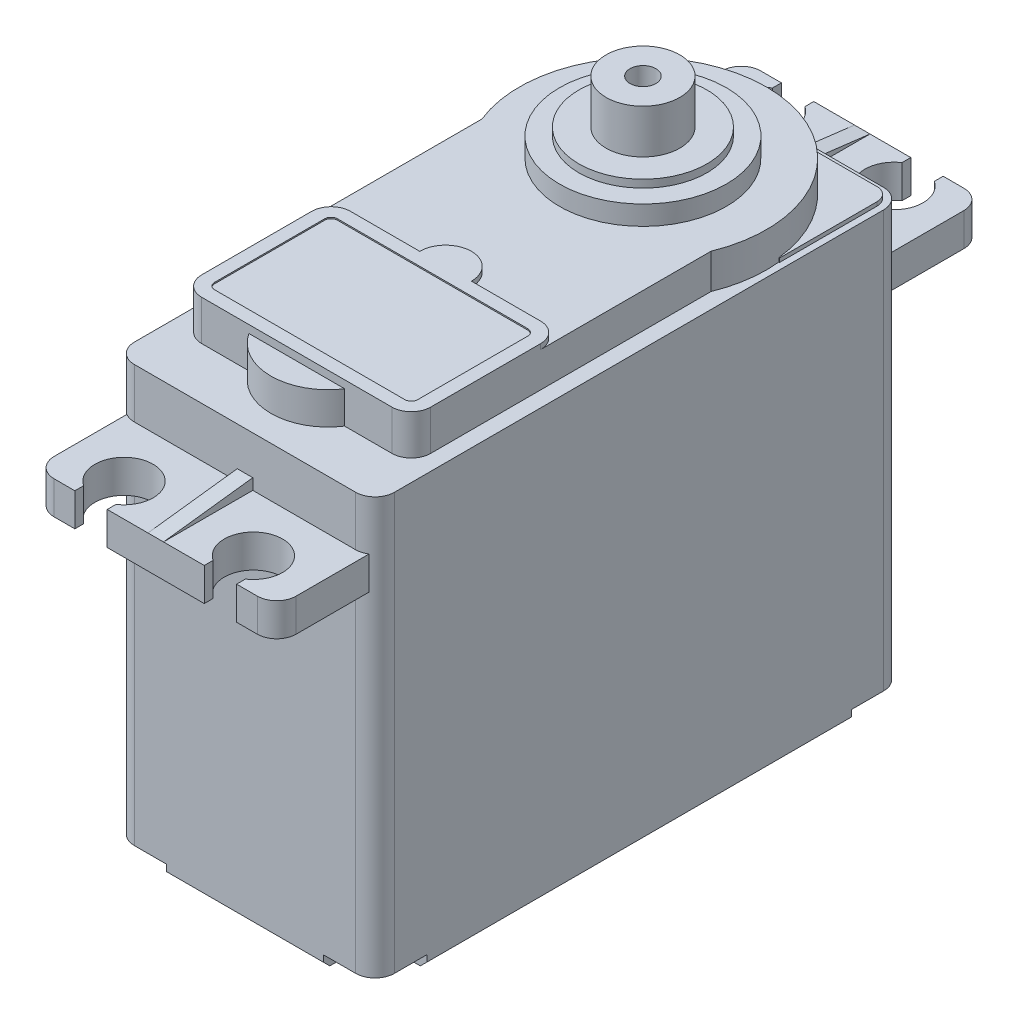
SolidWorks part; units mm, degrees
material "Feetech servo "
ref_plane "Front Plane" through (0, 0, 0) normal (0, 0, 1) x (1, 0, 0)
ref_plane "Top Plane" through (0, 0, 0) normal (0, 1, 0) x (1, 0, 0)
ref_plane "Right Plane" through (0, 0, 0) normal (1, 0, 0) x (0, 0, -1)
sketch "Sketch1" plane through (0, 0, 0) normal (0, 1, 0) x (1, 0, 0)
  line L0 (-10.05, -5.18) -> (10.05, -5.18) construction
  line L1 (-8.55, -25.58) -> (8.55, -25.58)
  line L2 (-10.05, -24.08) -> (-10.05, 13.72)
  line L3 (-8.55, 15.22) -> (8.55, 15.22)
  line L4 (10.05, -24.08) -> (10.05, 13.72)
  line L5 (-10.05, -25.58) -> (10.05, 15.22) construction
  line L6 (-10.05, 15.22) -> (10.05, -25.58) construction
  line L7 (0, -5.18) -> (0, 15.22) construction
  arc A0 (-10.05, 13.72) -> (-8.55, 15.22) centre (-8.55, 13.72) cw
  arc A1 (8.55, 15.22) -> (10.05, 13.72) centre (8.55, 13.72) cw
  arc A2 (10.05, -24.08) -> (8.55, -25.58) centre (8.55, -24.08) cw
  arc A3 (-8.55, -25.58) -> (-10.05, -24.08) centre (-8.55, -24.08) cw
  point P0 (0, 0)
  dimension "D5" = 1.5
  dimension "D1" = 20.1
  dimension "D2" = 40.8
  dimension "D3" = 25.58
extrude "Boss-Extrude1" add sketch "Sketch1" along normal blind 33.2
ref_plane "Plane1" through (0, 26.8, 0) normal (0, 1, 0) x (1, 0, 0)
sketch "Sketch4" plane through (0, 26.8, 0) normal (0, 1, 0) x (1, 0, 0)
  line L0 (-6.25, 22.12) -> (-6.25, 21.4408)
  line L1 (-7.85, -32.48) -> (-6.25, -32.48)
  line L2 (-9.35, -30.98) -> (-9.35, 20.62)
  line L3 (-7.85, 22.12) -> (-6.25, 22.12)
  line L4 (9.35, -30.98) -> (9.35, 20.62)
  line L5 (-9.35, -32.48) -> (9.35, 22.12) construction
  line L6 (-9.35, 22.12) -> (9.35, -32.48) construction
  line L7 (-3.75, 22.12) -> (-3.75, 21.4408)
  line L8 (-3.75, 22.12) -> (3.75, 22.12)
  line L9 (-10.05, -5.18) -> (10.05, -5.18) construction
  line L10 (6.25, 22.12) -> (7.85, 22.12)
  line L11 (6.25, -32.48) -> (6.25, -31.8008)
  line L12 (3.75, -32.48) -> (3.75, -31.8008)
  line L13 (0, -25.58) -> (0, 15.22) construction
  line L14 (-8.55, -25.58) -> (8.55, -25.58) construction
  line L15 (8.55, 15.22) -> (-8.55, 15.22) construction
  line L16 (-3.75, -32.48) -> (3.75, -32.48)
  line L17 (3.75, 22.12) -> (3.75, 21.4408)
  line L18 (6.25, 22.12) -> (6.25, 21.4408)
  line L19 (-3.75, -32.48) -> (-3.75, -31.8008)
  line L20 (-6.25, -32.48) -> (-6.25, -31.8008)
  line L21 (6.25, -32.48) -> (7.85, -32.48)
  line L22 (-10.05, 13.72) -> (-10.05, -24.08) construction
  arc A0 (7.85, 22.12) -> (9.35, 20.62) centre (7.85, 20.62) cw
  arc A1 (9.35, -30.98) -> (7.85, -32.48) centre (7.85, -30.98) cw
  arc A2 (-7.85, -32.48) -> (-9.35, -30.98) centre (-7.85, -30.98) cw
  arc A3 (-9.35, 20.62) -> (-7.85, 22.12) centre (-7.85, 20.62) cw
  arc A4 (-6.25, 21.4408) -> (-3.75, 21.4408) centre (-5, 19.57) ccw
  arc A5 (6.25, -31.8008) -> (3.75, -31.8008) centre (5, -29.93) ccw
  arc A6 (6.25, 21.4408) -> (3.75, 21.4408) centre (5, 19.57) cw
  arc A7 (-6.25, -31.8008) -> (-3.75, -31.8008) centre (-5, -29.93) cw
  point P0 (0, -5.18)
  dimension "D3" = 1.5
  dimension "D4" = 2.5
  dimension "D5" = 2.25
  dimension "D1" = 18.7
  dimension "D6" = 0.6792
  dimension "D7" = 10
  dimension "D8" = 49.5
extrude "Boss-Extrude2" add sketch "Sketch4" along normal blind 2.55
sketch "Sketch16" plane through (0, 33.2, 0) normal (0, 1, 0) x (1, 0, 0)
  line L0 (-9.55, 6.17) -> (9.55, 6.17)
  line L1 (0, 14.72) -> (0, -2.38) construction
  line L8 (-9.55, 13.72) -> (-9.55, -24.08)
  line L9 (-8.55, -25.08) -> (8.55, -25.08)
  line L10 (9.55, -24.08) -> (9.55, 13.72)
  line L11 (8.55, 14.72) -> (-8.55, 14.72)
  line L12 (-9.55, 13.72) -> (-9.55, -24.08)
  line L13 (-8.55, -25.08) -> (8.55, -25.08)
  line L14 (9.55, -24.08) -> (9.55, 13.72)
  line L15 (8.55, 14.72) -> (-8.55, 14.72)
  arc A8 (-8.55, 14.72) -> (-9.55, 13.72) centre (-8.55, 13.72) ccw
  arc A9 (-9.55, -24.08) -> (-8.55, -25.08) centre (-8.55, -24.08) ccw
  arc A10 (8.55, -25.08) -> (9.55, -24.08) centre (8.55, -24.08) ccw
  arc A11 (9.55, 13.72) -> (8.55, 14.72) centre (8.55, 13.72) ccw
  arc A12 (-8.55, 14.72) -> (-9.55, 13.72) centre (-8.55, 13.72) ccw
  arc A13 (-9.55, -24.08) -> (-8.55, -25.08) centre (-8.55, -24.08) ccw
  arc A14 (8.55, -25.08) -> (9.55, -24.08) centre (8.55, -24.08) ccw
  arc A15 (9.55, 13.72) -> (8.55, 14.72) centre (8.55, 13.72) ccw
  point P4 (0, 6.17)
  dimension "D1" = 0.5
extrude "Boss-Extrude11" add sketch "Sketch16" along normal blind 0.3 contours L1 L15 A12 L12 L0 | L15 L1 L0 L14 A15
sketch "Sketch5" plane through (0, 33.2, 0) normal (0, 1, 0) x (1, 0, 0)
  line L0 (8.55, -25.58) -> (-8.55, -25.58) construction
  line L1 (9.55, 6.17) -> (9.55, 13.72) construction
  line L2 (-8.85, 1.5811) -> (-8.85, -20.08)
  line L3 (-7.35, -21.58) -> (7.35, -21.58)
  line L4 (8.85, 1.5811) -> (8.85, -20.08)
  line L5 (-9.55, 13.72) -> (-9.55, 6.17) construction
  line L6 (0, 5.17) -> (0, -21.58) construction
  line L7 (8.55, 14.72) -> (-8.55, 14.72) construction
  arc A0 (8.85, 1.5811) -> (-8.85, 1.5811) centre (0, 5.17) ccw
  arc A1 (8.85, -20.08) -> (7.35, -21.58) centre (7.35, -20.08) cw
  arc A2 (-7.35, -21.58) -> (-8.85, -20.08) centre (-7.35, -20.08) cw
  dimension "D2" = 1.5
  dimension "D3" = 17.7
  dimension "D6" = 4
extrude "Boss-Extrude3" add sketch "Sketch5" along normal blind 2.7
sketch "Sketch6" plane through (0, 33.2, 0) normal (0, 1, 0) x (1, 0, 0)
  circle A0 centre (0, -19.1575) radius 4.4225
extrude "Boss-Extrude4" add sketch "Sketch6" along normal blind 2.5
sketch "Sketch7" plane through (0, 35.9, 0) normal (0, 1, 0) x (1, 0, 0)
  circle A0 centre (0, 5.17) radius 6.45
  arc A1 (8.85, 1.5811) -> (-8.85, 1.5811) centre (0, 5.17) ccw construction
  dimension "D1" = 12.9
extrude "Boss-Extrude5" add sketch "Sketch7" along normal blind 1.5
sketch "Sketch8" plane through (0, 37.4, 0) normal (0, 1, 0) x (1, 0, 0)
  circle A2 centre (0, 5.17) radius 4.95
  circle A3 centre (0, 5.17) radius 4.95
  dimension "D1" = 1.5
extrude "Boss-Extrude6" add sketch "Sketch8" along normal blind 0.6
sketch "Sketch10" plane through (0, 38, 0) normal (0, 1, 0) x (1, 0, 0)
  circle A1 centre (0, 5.17) radius 2.85
  dimension "D1" = 5.7
extrude "Boss-Extrude7" add sketch "Sketch10" along normal blind 3.4
sketch "Sketch12" plane through (0, 41.4, 0) normal (0, 1, 0) x (1, 0, 0)
  circle A0 centre (0, 5.17) radius 1
  dimension "D1" = 2
extrude "Cut-Extrude1" cut sketch "Sketch12" against normal blind 5
sketch "Sketch13" plane through (0, 35.9, 0) normal (0, 1, 0) x (1, 0, 0)
  line L0 (-8.85, 1.5811) -> (-8.85, -20.08) construction
  line L1 (-7.35, -21.58) -> (7.35, -21.58) construction
  line L2 (8.85, -20.08) -> (8.85, 1.5811) construction
  line L3 (-8.85, -11.58) -> (-8.85, -20.08)
  line L4 (-7.35, -21.58) -> (7.35, -21.58)
  line L5 (8.85, -20.08) -> (8.85, -11.58)
  line L6 (-7.85, -11.58) -> (-7.85, -20.08)
  line L7 (-7.35, -20.58) -> (7.35, -20.58)
  line L8 (7.85, -20.08) -> (7.85, -11.58)
  line L9 (-7.35, -11.08) -> (7.35, -11.08)
  line L10 (-7.35, -10.08) -> (-2, -10.08)
  line L11 (2, -10.08) -> (7.35, -10.08)
  line L12 (0, -10.08) -> (0, -11.08) construction
  arc A0 (-8.85, -20.08) -> (-7.35, -21.58) centre (-7.35, -20.08) ccw construction
  arc A1 (7.35, -21.58) -> (8.85, -20.08) centre (7.35, -20.08) ccw construction
  arc A2 (-8.85, -20.08) -> (-7.35, -21.58) centre (-7.35, -20.08) ccw
  arc A3 (7.35, -21.58) -> (8.85, -20.08) centre (7.35, -20.08) ccw
  arc A4 (-7.85, -20.08) -> (-7.35, -20.58) centre (-7.35, -20.08) ccw
  arc A5 (7.35, -20.58) -> (7.85, -20.08) centre (7.35, -20.08) ccw
  arc A6 (7.35, -11.08) -> (7.85, -11.58) centre (7.35, -11.58) cw
  arc A7 (-7.35, -11.08) -> (-7.85, -11.58) centre (-7.35, -11.58) ccw
  arc A8 (7.35, -10.08) -> (8.85, -11.58) centre (7.35, -11.58) cw
  arc A9 (-7.35, -10.08) -> (-8.85, -11.58) centre (-7.35, -11.58) ccw
  arc A10 (2, -10.08) -> (-2, -10.08) centre (0, -10.08) ccw
  point P8 (-7.85, 0.3518)
  point P15 (7.85, 0.3518)
  dimension "D2" = 0.5
  dimension "D1" = 1
  dimension "D3" = 1.5
  dimension "D4" = 4
  dimension "D5" = 9.5
extrude "Boss-Extrude9" add sketch "Sketch13" along normal blind 0.4
sketch "Sketch14" plane through (0, 35.9, 0) normal (0, 1, 0) x (1, 0, 0)
  line L3 (-7.85, -11.58) -> (-7.85, -20.08)
  line L4 (-7.85, -11.58) -> (-7.85, -20.08)
  line L5 (-7.35, -20.58) -> (7.35, -20.58)
  line L6 (-7.35, -20.58) -> (7.35, -20.58)
  line L7 (7.85, -20.08) -> (7.85, -11.58)
  line L8 (7.85, -20.08) -> (7.85, -11.58)
  line L10 (7.35, -11.08) -> (-7.35, -11.08)
  line L11 (7.35, -11.08) -> (-7.35, -11.08)
  arc A3 (-7.85, -20.08) -> (-7.35, -20.58) centre (-7.35, -20.08) ccw
  arc A4 (-7.85, -20.08) -> (-7.35, -20.58) centre (-7.35, -20.08) ccw
  arc A5 (7.35, -20.58) -> (7.85, -20.08) centre (7.35, -20.08) ccw
  arc A6 (7.35, -20.58) -> (7.85, -20.08) centre (7.35, -20.08) ccw
  arc A7 (7.85, -11.58) -> (7.35, -11.08) centre (7.35, -11.58) ccw
  arc A8 (7.85, -11.58) -> (7.35, -11.08) centre (7.35, -11.58) ccw
  arc A10 (-7.35, -11.08) -> (-7.85, -11.58) centre (-7.35, -11.58) ccw
  arc A11 (-7.35, -11.08) -> (-7.85, -11.58) centre (-7.35, -11.58) ccw
  dimension "D1" = 0
extrude "Boss-Extrude10" add sketch "Sketch14" along normal blind 0.3
chamfer "Chamfer1" distance 0.5 angle 45 8 edges at (-10.05, 0, 5.18) (-9.6107, 0, 25.1407) (0, 0, 25.58) (9.6107, 0, 25.1407) (10.05, 0, 5.18) (9.6107, 0, -14.7807) (0, 0, -15.22) (-9.6107, 0, -14.7807)
sketch "Sketch17" plane through (0, 0, 0) normal (0, -1, 0) x (1, 0, 0)
  line L0 (-10.05, -13.72) -> (-10.05, 24.08) construction
  line L1 (-8.55, 25.58) -> (8.55, 25.58) construction
  line L3 (-10.05, 21.58) -> (-10.05, 24.08)
  line L4 (-8.55, 25.58) -> (-6.05, 25.58)
  line L5 (-6.05, 25.58) -> (-6.05, 23.08)
  line L6 (-7.55, 21.58) -> (-10.05, 21.58)
  arc A0 (-8.55, 25.58) -> (-10.05, 24.08) centre (-8.55, 24.08) ccw construction
  arc A3 (-8.55, 25.58) -> (-10.05, 24.08) centre (-8.55, 24.08) ccw
  arc A4 (-6.05, 23.08) -> (-7.55, 21.58) centre (-7.55, 23.08) cw
  point P10 (-6.05, 21.58)
  dimension "D3" = 1.5
  dimension "D1" = 4
  dimension "D2" = 4
extrude "Cut-Extrude2" cut sketch "Sketch17" against normal blind 1
mirror "Mirror1" about plane through (0, 0, 0) normal (1, 0, 0) of "Cut-Extrude2"
ref_plane "Plane2" through (0, 0, 5.18) normal (0, 0, 1) x (1, 0, 0)
mirror "Mirror2" about plane through (0, 0, 5.18) normal (0, 0, 1) of "Mirror1", "Cut-Extrude2"
sketch "Sketch19" plane through (0, 0, 0) normal (1, 0, 0) x (0, 0, -1)
  line L0 (-25.58, 30.2) -> (-25.58, 29.35)
  line L1 (-25.58, 33.2) -> (-25.58, 29.35) construction
  line L2 (-25.58, 29.35) -> (-32.48, 29.35)
  line L3 (-32.48, 29.35) -> (-25.58, 30.2)
  line L4 (15.22, 30.2) -> (15.22, 29.35)
  line L5 (15.22, 33.2) -> (15.22, 29.35) construction
  line L6 (14.9889, 29.35) -> (20.62, 29.35) construction
  line L7 (15.22, 29.35) -> (22.12, 29.35)
  line L8 (22.12, 29.35) -> (15.22, 30.2)
  dimension "D1" = 0.85
extrude "Boss-Extrude12" add sketch "Sketch19" along normal mid plane 1.2
